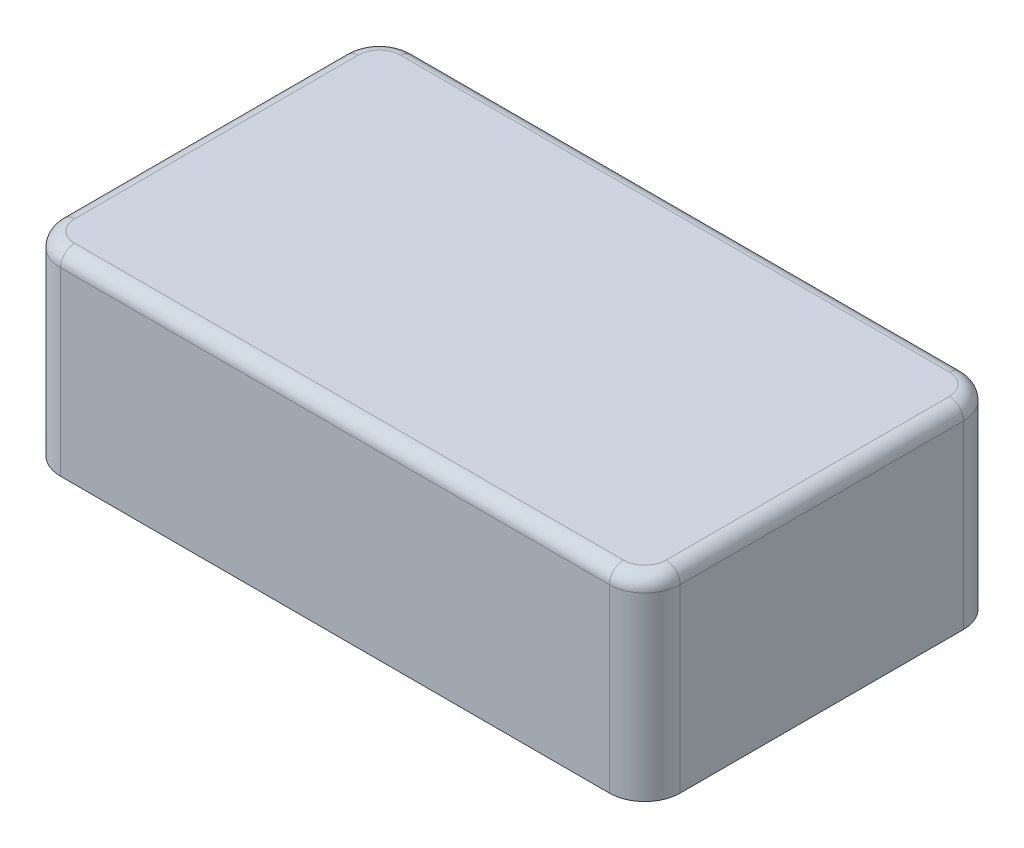
SolidWorks part; units mm, degrees
ref_plane "Plan de face" through (0, 0, 0) normal (0, 0, 1) x (1, 0, 0)
ref_plane "Plan de dessus" through (0, 0, 0) normal (0, 1, 0) x (1, 0, 0)
ref_plane "Plan de droite" through (0, 0, 0) normal (1, 0, 0) x (0, 0, -1)
sketch "Esquisse1" plane through (0, 0, 0) normal (0, 1, 0) x (1, 0, 0)
  line L1 (1.55, -1) -> (-1.55, -1)
  line L2 (1.75, -0.8) -> (1.75, 0.8)
  line L3 (1.55, 1) -> (-1.55, 1)
  line L4 (-1.75, -0.8) -> (-1.75, 0.8)
  line L5 (1.75, -1) -> (-1.75, 1) construction
  line L6 (1.75, 1) -> (-1.75, -1) construction
  arc A0 (1.75, 0.8) -> (1.55, 1) centre (1.55, 0.8) ccw
  arc A1 (1.55, -1) -> (1.75, -0.8) centre (1.55, -0.8) ccw
  arc A2 (-1.55, -1) -> (-1.75, -0.8) centre (-1.55, -0.8) cw
  arc A3 (-1.55, 1) -> (-1.75, 0.8) centre (-1.55, 0.8) ccw
  point P0 (0, 0)
  dimension "D3" = 0.2
  dimension "D1" = 2
  dimension "D2" = 3.5
extrude "Boss.-Extru.1" add sketch "Esquisse1" along normal blind 1.1
fillet "Congé1" radius 0.08 8 edges at (1.75, 1.1, 0) (1.6914, 1.1, 0.9414) (0, 1.1, 1) (-1.6914, 1.1, 0.9414) (-1.75, 1.1, 0) (-1.6914, 1.1, -0.9414) (0, 1.1, -1) (1.6914, 1.1, -0.9414)
equation "\"é\"=61.6442"
